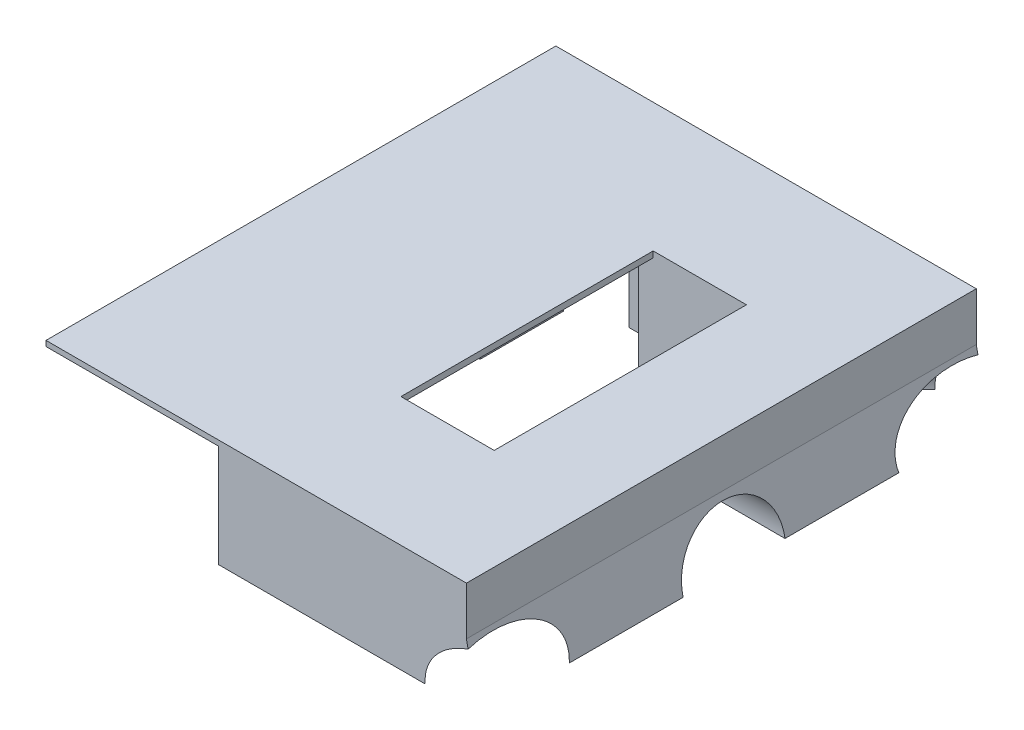
SolidWorks part; units mm, degrees
ref_plane "Front Plane" through (0, 0, 0) normal (0, 0, 1) x (1, 0, 0)
ref_plane "Top Plane" through (0, 0, 0) normal (0, 1, 0) x (1, 0, 0)
ref_plane "Right Plane" through (0, 0, 0) normal (1, 0, 0) x (0, 0, -1)
sketch "Sketch1" plane through (0, 0, 0) normal (0, 1, 0) x (1, 0, 0)
  line L1 (-55.9466, 49.5438) -> (39.0534, 49.5438)
  line L2 (-55.9466, 49.5438) -> (-55.9466, -45.4562)
  line L3 (-55.9466, -45.4562) -> (39.0534, -45.4562)
  line L4 (39.0534, 49.5438) -> (39.0534, -45.4562)
  dimension "D1" = 95
  dimension "D2" = 95
extrude "Boss-Extrude1" add sketch "Sketch1" along normal blind 50
sketch "Sketch2" plane through (0, 0, 45.4562) normal (0, 0, 1) x (1, 0, 0)
  line L0 (39.0534, 0) -> (36.3534, 50)
  line L1 (-55.9466, 50) -> (39.0534, 50) construction
  line L2 (36.3534, 50) -> (39.0534, 50)
  line L3 (39.0534, 50) -> (39.0534, 0)
  dimension "D1" = 2.7
extrude "Cut-Extrude1" cut sketch "Sketch2" against normal blind 100
sketch "Sketch3" plane through (38.9399, 2.1028, 0) normal (0.9985, 0.0539, 0) x (0, 0, -1)
  line L0 (-45.4562, 47.967) -> (-45.4562, -2.1058) construction
  line L1 (-45.4562, -2.1058) -> (49.5438, -2.1058) construction
  circle A0 centre (2.0438, 13.3942) radius 9.5
  point P4 (2.0438, -2.1058)
  dimension "D3" = 19
  dimension "D1" = 47.5
  dimension "D2" = 15.5
extrude "Cut-Extrude2" cut sketch "Sketch3" against normal blind 45
sketch "Sketch5" plane through (0, 50, 0) normal (0, 1, 0) x (1, 0, 0)
  line L0 (39.0534, 49.5438) -> (39.0534, 29.5438)
  line L1 (39.0534, -45.4562) -> (39.0534, 49.5438) construction
  line L2 (39.0534, 29.5438) -> (19.0534, 49.5438)
  line L3 (19.0534, 49.5438) -> (39.0534, 49.5438)
  line L4 (39.0534, -45.4562) -> (39.0534, -25.4562)
  line L5 (39.0534, -25.4562) -> (19.0534, -45.4562)
  line L6 (-55.9466, -45.4562) -> (36.3534, -45.4562) construction
  line L7 (19.0534, -45.4562) -> (39.0534, -45.4562)
  dimension "D1" = 20
  dimension "D2" = 20
  dimension "D3" = 20
  dimension "D4" = 20
extrude "Cut-Extrude4" cut sketch "Sketch5" against normal blind 45
sketch "Sketch6" plane through (0, 50, 0) normal (0, 1, 0) x (1, 0, 0)
  line L0 (19.0534, -45.4562) -> (12.9256, -39.3283)
  line L1 (12.9256, -39.3283) -> (6.7977, -45.4562)
  line L2 (-55.9466, -45.4562) -> (19.0534, -45.4562) construction
  line L3 (6.7977, -45.4562) -> (19.0534, -45.4562)
  line L4 (19.0534, 49.5438) -> (12.9256, 43.4159)
  line L5 (12.9256, 43.4159) -> (6.7977, 49.5438)
  line L6 (19.0534, 49.5438) -> (-55.9466, 49.5438) construction
  line L7 (6.7977, 49.5438) -> (19.0534, 49.5438)
extrude "Cut-Extrude5" cut sketch "Sketch6" against normal blind 45
sketch "Sketch7" plane through (-13.2014, 0, 13.2014) normal (-0.7071, 0, 0.7071) x (0.7071, 0, 0.7071)
  line L0 (45.6152, 5) -> (42.9152, 50)
  line L1 (45.6152, 50) -> (36.9491, 50) construction
  line L2 (42.9152, 50) -> (45.6152, 50)
  line L3 (45.6152, 50) -> (45.6152, 5)
  dimension "D1" = 2.7
extrude "Cut-Extrude6" cut sketch "Sketch7" against normal blind 45
sketch "Sketch8" plane through (-15.2452, 0, -15.2452) normal (-0.7071, 0, -0.7071) x (-0.7071, 0, 0.7071)
  line L0 (-48.5056, 5) -> (-45.8056, 50)
  line L1 (-39.8395, 50) -> (-48.5056, 50) construction
  line L2 (-45.8056, 50) -> (-48.5056, 50)
  line L3 (-48.5056, 50) -> (-48.5056, 5)
  dimension "D1" = 2.7
extrude "Cut-Extrude7" cut sketch "Sketch8" against normal blind 45
sketch "Sketch9" plane through (34.387, 2.9178, -34.387) normal (0.7058, 0.0599, -0.7058) x (-0.7084, 0.0597, -0.7033)
  line L1 (-6.2064, 2.4614) -> (-2.7761, 47.4176) construction
  line L2 (7.1802, -4.1889) -> (74.4757, -4.1889) construction
  circle A0 centre (14.527, 11.3111) radius 9.5
  dimension "D1" = 15.5
  dimension "D2" = 20
extrude "Cut-Extrude9" cut sketch "Sketch9" against normal blind 45
sketch "Sketch11" plane through (32.3505, 2.745, 32.3505) normal (0.7058, 0.0599, 0.7058) x (0.7033, 0.0597, -0.7084)
  line L0 (11.3114, 46.7473) -> (9.3514, 1.703) construction
  line L1 (-71.5478, 4.7302) -> (-4.7333, -3.3019) construction
  circle A0 centre (-10.1775, 12.9642) radius 9.5
  dimension "D1" = 20
  dimension "D2" = 15.5
extrude "Cut-Extrude10" cut sketch "Sketch11" against normal blind 45
sketch "Sketch12" plane through (0, 5, 0) normal (0, 1, 0) x (1, 0, 0)
  line L1 (38.7834, -45.4562) -> (6.7977, -45.4562)
  line L2 (38.7834, -45.4562) -> (38.7834, 49.5438)
  line L3 (38.7834, 49.5438) -> (6.7977, 49.5438)
  line L4 (6.7977, -45.4562) -> (6.7977, 49.5438)
extrude "Boss-Extrude2" add sketch "Sketch12" along normal blind 45
sketch "Sketch13" plane through (0, 0, 45.4562) normal (0, 0, 1) x (1, 0, 0)
  line L0 (39.0534, 0) -> (29.0534, 3)
  line L1 (29.0534, 3) -> (19.0534, 50)
  line L2 (-55.9466, 50) -> (38.7834, 50) construction
  line L3 (19.0534, 50) -> (49.7453, 50)
  line L4 (49.7453, 50) -> (39.0534, 0)
  line L5 (-55.9466, 0) -> (39.0534, 0) construction
  dimension "D1" = 10
  dimension "D2" = 3
  dimension "D3" = 10
extrude "Cut-Extrude11" cut sketch "Sketch13" against normal blind 100
sketch "Sketch14" plane through (-5.9946, -0.3237, 0) normal (0.9985, 0.0539, 0) x (0, 0, -1)
  circle A0 centre (2.0438, 13.3942) radius 9.5
extrude "Cut-Extrude12" cut sketch "Sketch14" along normal blind 100
sketch "Sketch15" plane through (0.5878, 0.0499, 0.5878) normal (0.7058, 0.0599, 0.7058) x (0.7033, 0.0597, -0.7084)
  circle A0 centre (-10.1775, 12.9642) radius 9.5
extrude "Cut-Extrude13" cut sketch "Sketch15" along normal blind 100
sketch "Sketch16" plane through (2.6243, 0.2227, -2.6243) normal (0.7058, 0.0599, -0.7058) x (-0.7084, 0.0597, -0.7033)
  circle A0 centre (14.527, 11.3111) radius 9.5
extrude "Cut-Extrude14" cut sketch "Sketch16" along normal blind 100
fillet "Fillet2" radius 4 1 edges at (29.0534, 3, -2.0438)
sketch "Sketch17" plane through (0, 0, 45.4562) normal (0, 0, 1) x (1, 0, 0)
  line L3 (-55.9466, 0) -> (-21.9466, 0)
  line L4 (-55.9466, 0) -> (-55.9466, 34)
  line L5 (-55.9466, 34) -> (-21.9466, 34)
  line L6 (-21.9466, 0) -> (-21.9466, 34)
  dimension "D1" = 34
  dimension "D2" = 34
extrude "Cut-Extrude16" cut sketch "Sketch17" against normal blind 22
sketch "Sketch19" plane through (0, 0, -49.5438) normal (0, 0, -1) x (-1, 0, 0)
  line L1 (55.9466, 0) -> (21.9466, 0)
  line L2 (55.9466, 0) -> (55.9466, 34)
  line L3 (55.9466, 34) -> (21.9466, 34)
  line L4 (21.9466, 0) -> (21.9466, 34)
  dimension "D1" = 34
  dimension "D2" = 34
extrude "Cut-Extrude17" cut sketch "Sketch19" against normal blind 22
sketch "Sketch20" plane through (0, 0, 23.4562) normal (0, 0, 1) x (1, 0, 0)
  line L0 (-55.9466, 0) -> (-21.9466, 0) construction
  line L1 (-45.1966, 20.5) -> (-32.6966, 20.5)
  line L2 (-45.1966, 20.5) -> (-45.1966, 4)
  line L3 (-45.1966, 4) -> (-32.6966, 4)
  line L4 (-32.6966, 20.5) -> (-32.6966, 4)
  line L5 (-55.9466, 34) -> (-55.9466, 0) construction
  line L6 (-21.9466, 0) -> (-21.9466, 34) construction
  dimension "D1" = 12.5
  dimension "D2" = 16.5
  dimension "D3" = 4
  dimension "D4" = 10.75
  dimension "D5" = 10.75
extrude "Cut-Extrude18" cut sketch "Sketch20" against normal blind 60
sketch "Sketch21" plane through (0, 0, 23.4562) normal (0, 0, 1) x (1, 0, 0)
  line L0 (-55.9466, 34) -> (-48.4466, 0)
  line L1 (-55.9466, 0) -> (-21.9466, 0) construction
  line L2 (-48.4466, 0) -> (-55.9466, 0)
  line L3 (-55.9466, 0) -> (-55.9466, 34)
  dimension "D1" = 7.5
extrude "Cut-Extrude19" cut sketch "Sketch21" against normal blind 60
sketch "Sketch22" plane through (0, 0, 45.4562) normal (0, 0, 1) x (1, 0, 0)
  line L6 (-57.7624, 14.4177) -> (42.054, 14.4177)
  line L7 (-57.7624, 14.4177) -> (-57.7624, -11.9499)
  line L8 (-57.7624, -11.9499) -> (42.054, -11.9499)
  line L9 (42.054, 14.4177) -> (42.054, -11.9499)
extrude "Cut-Extrude21" cut sketch "Sketch22" against normal blind 100
sketch "Sketch23" plane through (0, 14.4177, 0) normal (0, -1, 0) x (-1, 0, 0)
  line L0 (-16.5817, -45.4562) -> (21.9466, -45.4562) construction
  line L1 (21.9466, -23.4562) -> (21.9466, -45.4562) construction
  line L2 (-16.5817, 49.5438) -> (21.9466, 49.5438) construction
  line L3 (-26.6241, -28.6586) -> (-26.6241, -7.4463) construction
  line L4 (-26.6241, 11.5339) -> (-26.6241, 32.7462) construction
  line L6 (21.9466, 49.5438) -> (21.9466, 27.5438) construction
  circle A0 centre (11.9466, -35.4562) radius 1
  circle A1 centre (11.9466, 39.5438) radius 1
  circle A2 centre (-16.6241, -12.9562) radius 1
  circle A3 centre (-16.6241, 17.0438) radius 1
  ellipse E0 centre (-26.5329, 2.0438) end of major axis (-26.5329, 11.5438) minor radius 2.0012 (-26.6241, -7.4463) -> (-26.6241, 11.5339) ccw construction
  point P23 (-24.5317, 2.0438)
  dimension "D1" = 10
  dimension "D3" = 10
  dimension "D4" = 15
  dimension "D6" = 15
  dimension "D2" = 10
  dimension "D5" = 10
  dimension "D7" = 10
  dimension "D8" = 10
extrude "Cut-Extrude24" cut sketch "Sketch23" against normal blind 909
sketch "Sketch25" plane through (0, 14.4177, 0) normal (0, -1, 0) x (-1, 0, 0)
  line L0 (51.6269, -23.4562) -> (45.1966, -23.4562) construction
  line L1 (45.1966, -23.4562) -> (45.1966, 27.5438) construction
  line L2 (51.6269, 27.5438) -> (45.1966, 27.5438) construction
  circle A0 centre (48.1966, -13.4562) radius 1
  circle A1 centre (48.1966, 17.5438) radius 1
  point P8 (48.4117, 27.5438)
  dimension "D1" = 10
  dimension "D3" = 10
  dimension "D2" = 3
extrude "Cut-Extrude25" cut sketch "Sketch25" against normal blind 789
sketch "Sketch27" plane through (0, 14.4177, 0) normal (0, -1, 0) x (-1, 0, 0)
  line L0 (32.6966, 27.5438) -> (32.6966, -23.4562) construction
  line L1 (30.6966, -21.4562) -> (4.5669, -21.4562)
  line L2 (30.6966, -21.4562) -> (30.6966, 25.5438)
  line L3 (30.6966, 25.5438) -> (4.5669, 25.5438)
  line L4 (4.5669, -21.4562) -> (4.5669, 25.5438)
  dimension "D1" = 2
  dimension "D2" = 2
  dimension "D3" = 2
  dimension "D4" = 0
extrude "Cut-Extrude27" cut sketch "Sketch27" against normal blind 9
sketch "Sketch28" plane through (0, 14.4177, 0) normal (0, -1, 0) x (-1, 0, 0)
  line L0 (30.6966, -21.4562) -> (30.6966, 25.5438) construction
  line L1 (30.6966, -7.9562) -> (32.6966, -7.9562)
  line L2 (30.6966, -7.9562) -> (30.6966, 12.0438)
  line L3 (30.6966, 12.0438) -> (32.6966, 12.0438)
  line L4 (32.6966, -7.9562) -> (32.6966, 12.0438)
  line L5 (32.6966, 27.5438) -> (32.6966, -23.4562) construction
  dimension "D1" = 20
  dimension "D2" = 15.5
  dimension "D3" = 15.5
extrude "Cut-Extrude28" cut sketch "Sketch28" against normal blind 5
sketch "Sketch29" plane through (0, 0, 45.4562) normal (0, 0, 1) x (1, 0, 0)
  line L1 (-55.9466, 34) -> (43.0708, 34)
  line L2 (-55.9466, 34) -> (-55.9466, 51.8973)
  line L3 (-55.9466, 51.8973) -> (43.0708, 51.8973)
  line L4 (43.0708, 34) -> (43.0708, 51.8973)
extrude "Cut-Extrude29" cut sketch "Sketch29" against normal blind 447
sketch "Sketch30" plane through (0, 0, 45.4562) normal (0, 0, 1) x (1, 0, 0)
  line L0 (24.2586, 25.5358) -> (-54.0795, 25.5358)
  line L1 (22.4577, 34) -> (24.5777, 24.0358) construction
  line L2 (-51.6269, 14.4177) -> (-55.9466, 34) construction
  line L3 (-54.0795, 25.5358) -> (-55.9466, 34)
  line L4 (-55.9466, 34) -> (22.4577, 34)
  line L5 (22.4577, 34) -> (24.2586, 25.5358)
  dimension "D1" = 1.5
extrude "Cut-Extrude30" cut sketch "Sketch30" against normal blind 447
sketch "Sketch31" plane through (0, 23.4177, 0) normal (0, -1, 0) x (-1, 0, 0)
  line L1 (30.6966, -21.4562) -> (4.5669, -21.4562)
  line L2 (30.6966, -21.4562) -> (30.6966, 25.5438)
  line L3 (30.6966, 25.5438) -> (4.5669, 25.5438)
  line L4 (4.5669, -21.4562) -> (4.5669, 25.5438)
extrude "Cut-Extrude31" cut sketch "Sketch31" against normal blind 447
sketch "Sketch32" plane through (0, 14.4177, 0) normal (0, -1, 0) x (-1, 0, 0)
  line L0 (30.6966, 25.5438) -> (7.283, 25.5438) construction
  line L1 (7.283, -21.4562) -> (-5.4331, -21.4562)
  line L2 (7.283, -21.4562) -> (7.283, 25.5438)
  line L3 (7.283, 25.5438) -> (-5.4331, 25.5438)
  line L4 (-5.4331, -21.4562) -> (-5.4331, 25.5438)
  dimension "D1" = 0
  dimension "D2" = 10
extrude "Cut-Extrude32" cut sketch "Sketch32" against normal blind 90
sketch "Sketch35" plane through (0, 25.5358, 0) normal (0, 1, 0) x (1, 0, 0)
  line L0 (-54.0795, 27.5438) -> (-21.9466, 27.5438)
  line L1 (-21.9466, 27.5438) -> (-21.9466, 49.5438)
  line L2 (-21.9466, 49.5438) -> (24.2586, 49.5438)
  line L3 (24.2586, 49.5438) -> (24.2586, -45.4562)
  line L4 (24.2586, -45.4562) -> (-21.9466, -45.4562)
  line L5 (-21.9466, -45.4562) -> (-21.9466, -23.4562)
  line L6 (-21.9466, -23.4562) -> (-54.0795, -23.4562)
  line L7 (-54.0795, -23.4562) -> (-54.0795, 27.5438)
extrude "Boss-Extrude4" add sketch "Sketch35" along normal blind 9
sketch "Sketch37" plane through (0, 25.5358, 0) normal (0, -1, 0) x (-1, 0, 0)
  line L1 (30.6966, -21.4562) -> (-5.4331, -21.4562)
  line L2 (30.6966, -21.4562) -> (30.6966, 25.5438)
  line L3 (30.6966, 25.5438) -> (-5.4331, 25.5438)
  line L4 (-5.4331, -21.4562) -> (-5.4331, 25.5438)
extrude "Cut-Extrude34" cut sketch "Sketch37" against normal blind 9
sketch "Sketch38" plane through (0, 14.4177, 0) normal (0, -1, 0) x (-1, 0, 0)
  line L0 (32.6966, -23.4562) -> (21.9466, -23.4562) construction
  line L1 (30.6966, -26.9562) -> (14.6966, -26.9562)
  line L2 (30.6966, -26.9562) -> (30.6966, 31.0438)
  line L3 (30.6966, 31.0438) -> (14.6966, 31.0438)
  line L4 (14.6966, -26.9562) -> (14.6966, 31.0438)
  line L5 (32.6966, 27.5438) -> (21.9466, 27.5438) construction
  point P4 (27.3216, -23.4562)
  dimension "D1" = 3.5
  dimension "D2" = 58
  dimension "D3" = 3.5
  dimension "D4" = 0
  dimension "D5" = 16
extrude "Cut-Extrude36" cut sketch "Sketch38" against normal blind 19
sketch "Sketch40" plane through (0, 0, -25.5438) normal (0, 0, 1) x (1, 0, 0)
  line L0 (-14.6966, 33.4177) -> (-30.6966, 33.4177) construction
  line L1 (-30.6966, 34.5358) -> (-21.9466, 34.5358)
  line L2 (-30.6966, 34.5358) -> (-30.6966, 33.4177)
  line L3 (-30.6966, 33.4177) -> (-21.9466, 33.4177)
  line L4 (-21.9466, 34.5358) -> (-21.9466, 33.4177)
  dimension "D1" = 0
extrude "Boss-Extrude5" add sketch "Sketch40" along normal blind 48
sketch "Sketch41" plane through (-21.9466, 0, 0) normal (1, 0, 0) x (0, 0, -1)
  line L1 (-21.4562, 33.4177) -> (25.5438, 33.4177)
  line L2 (-21.4562, 33.4177) -> (-21.4562, 34.5358)
  line L3 (-21.4562, 34.5358) -> (25.5438, 34.5358)
  line L4 (25.5438, 33.4177) -> (25.5438, 34.5358)
extrude "Boss-Extrude6" add sketch "Sketch41" along normal blind 10
sketch "Sketch42" plane through (0, 0, 23.4562) normal (0, 0, 1) x (1, 0, 0)
  line L1 (-54.0795, 34.5358) -> (-54.0795, 25.5358) construction
  line L2 (-54.0795, 33.5358) -> (-21.9466, 33.5358)
  line L3 (-54.0795, 33.5358) -> (-54.0795, 34.5358)
  line L4 (-54.0795, 34.5358) -> (-21.9466, 34.5358)
  line L5 (-21.9466, 33.5358) -> (-21.9466, 34.5358)
  dimension "D1" = 1
extrude "Boss-Extrude7" add sketch "Sketch42" along normal blind 22
sketch "Sketch43" plane through (0, 0, -27.5438) normal (0, 0, -1) x (-1, 0, 0)
  line L1 (21.9466, 33.4177) -> (54.0795, 33.4177)
  line L2 (21.9466, 33.4177) -> (21.9466, 34.5358)
  line L3 (21.9466, 34.5358) -> (54.0795, 34.5358)
  line L4 (54.0795, 33.4177) -> (54.0795, 34.5358)
extrude "Boss-Extrude8" add sketch "Sketch43" along normal blind 22
